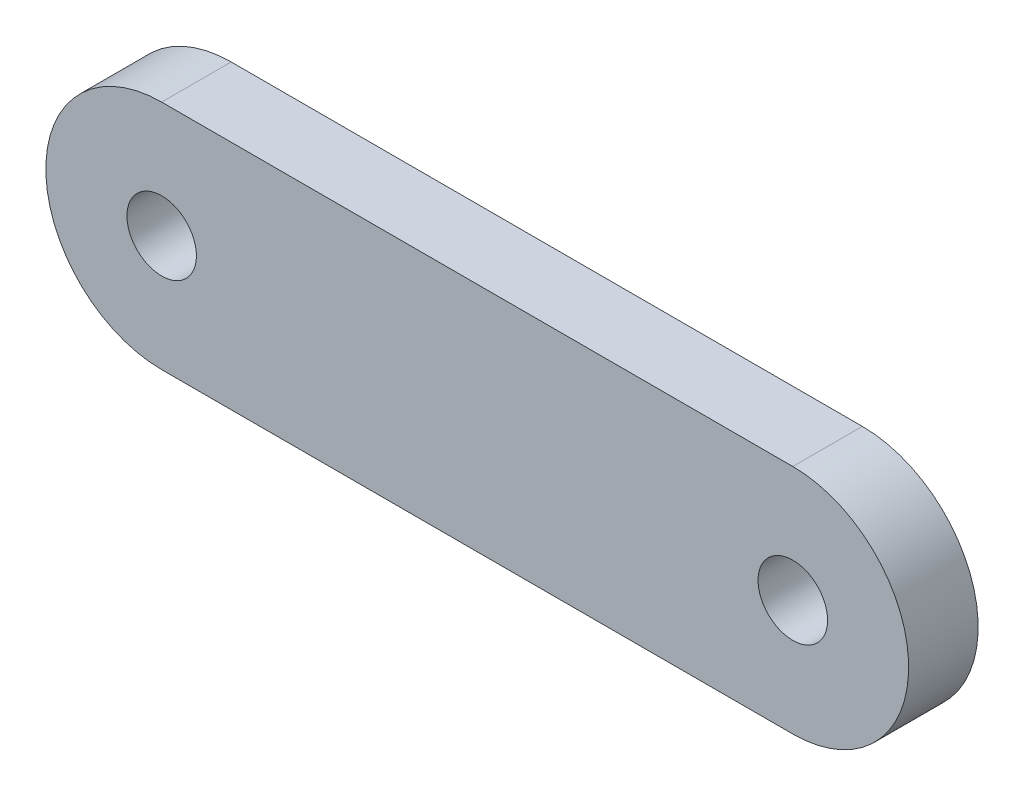
SolidWorks part; units mm, degrees
ref_plane "前基準面" through (0, 0, 0) normal (0, 0, 1) x (1, 0, 0)
ref_plane "上基準面" through (0, 0, 0) normal (0, 1, 0) x (1, 0, 0)
ref_plane "右基準面" through (0, 0, 0) normal (1, 0, 0) x (0, 0, -1)
sketch "草圖1" plane through (0, 0, 0) normal (0, 0, 1) x (1, 0, 0)
  line L0 (-6.81, 0) -> (6.81, 0) construction
  line L1 (-6.81, 2.5) -> (6.81, 2.5)
  line L2 (-6.81, -2.5) -> (6.81, -2.5)
  arc A0 (-6.81, 2.5) -> (-6.81, -2.5) centre (-6.81, 0) ccw
  arc A1 (6.81, -2.5) -> (6.81, 2.5) centre (6.81, 0) ccw
  circle A2 centre (-6.81, 0) radius 0.75
  circle A3 centre (6.81, 0) radius 0.75
  point P3 (0, 0)
  dimension "D1" = 2.5
  dimension "D3" = 1.5
  dimension "D2" = 13.62
extrude "填料-伸長1" add sketch "草圖1" along normal mid plane 1.5
